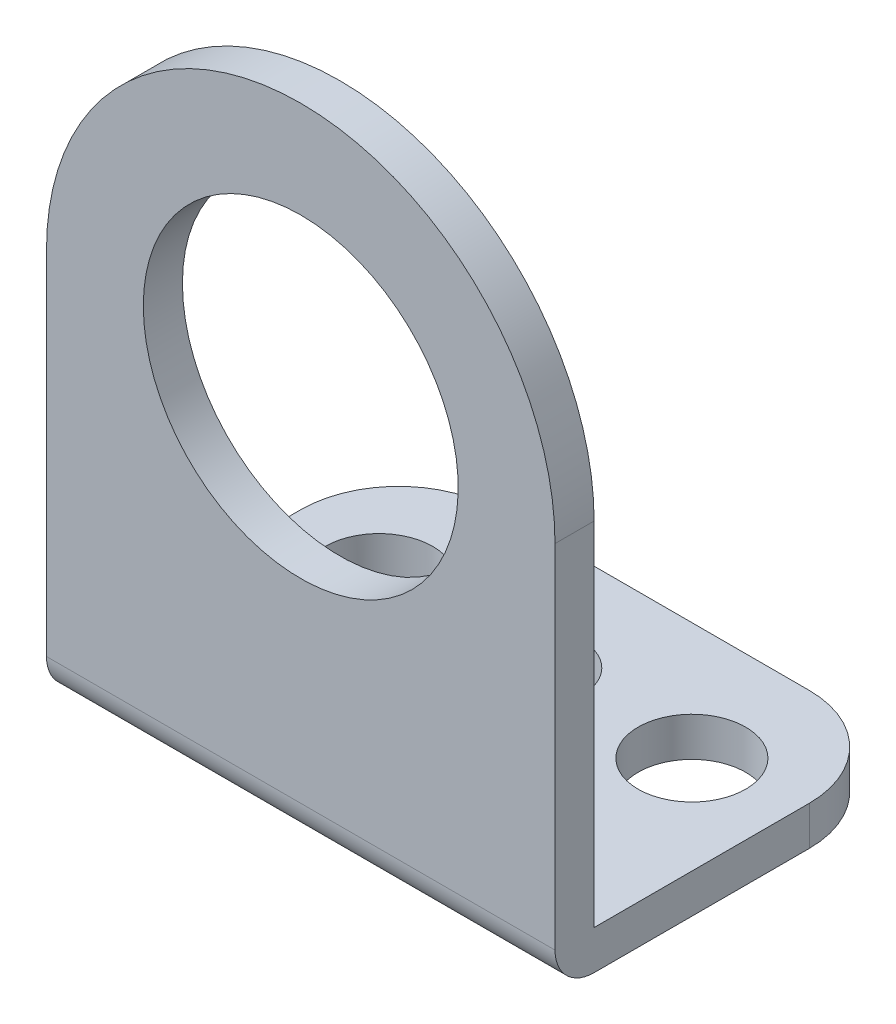
SolidWorks part; units mm, degrees
material "Al 6201"
ref_plane "Front Plane" through (0, 0, 0) normal (0, 0, 1) x (1, 0, 0)
ref_plane "Top Plane" through (0, 0, 0) normal (0, 1, 0) x (1, 0, 0)
ref_plane "Right Plane" through (0, 0, 0) normal (1, 0, 0) x (0, 0, -1)
sketch "Sketch1" plane through (0, 0, 0) normal (1, 0, 0) x (0, 0, -1)
  line L1 (0, 7.5) -> (2, 7.5)
  line L2 (0, 7.5) -> (0, 0)
  line L4 (2, 7.5) -> (2, 2)
  line L5 (2, 2) -> (18, 2)
  line L7 (0, 0) -> (18, 0)
  line L8 (18, 2) -> (18, 0)
  dimension "D1" = 7.5
  dimension "D2" = 18
  dimension "D3" = 2
extrude "Boss-Extrude1" add sketch "Sketch1" along normal mid plane 26
sketch "Sketch12" plane through (0, 0, -2) normal (0, 0, -1) x (-1, 0, 0)
  line L1 (0, 0) -> (0, 50000) construction
  line L3 (-13, 7.5) -> (13, 7.5) construction
  line L4 (-13, 0) -> (13, 0) construction
  line L6 (0, 20) -> (14.6033, 20) construction
  line L7 (0, 20) -> (-14.6033, 20) construction
  line L8 (13, 20) -> (13, 7.5)
  line L9 (13, 7.5) -> (-13, 7.5)
  line L10 (-13, 7.5) -> (-13, 20)
  circle A1 centre (0, 20) radius 8.05
  arc A2 (-13, 20) -> (13, 20) centre (0, 20) cw
  point P15 (0, 7.5)
  dimension "D3" = 16.1
  dimension "D1" = 20
extrude "Boss-Extrude2" add sketch "Sketch12" against normal up to surface (2 mm away) up to face at (0, 3.75, 0)
fillet "Fillet3" radius 2 1 edges at (0, 0, 0)
sketch "Sketch4" plane through (0, 0, -2) normal (0, 0, -1) x (-1, 0, 0)
  line L2 (0, 0) -> (0, 50000) construction
ref_plane "Plane1" through (0, 0, 0) normal (0, 0.7071, 0.7071) x (-1, 0, 0)
sketch "Sketch14" plane through (0, 0, 0) normal (0, 0.7071, 0.7071) x (-1, 0, 0)
  line L0 (0, 0) -> (0, 50000) construction
  line L1 (8.5, -2.8284) -> (11, -7.1586)
  line L2 (11, -7.1586) -> (13.5, -2.8284)
  line L3 (-13, -2.8284) -> (13, -2.8284) construction
  line L4 (8.5, -2.8284) -> (13.5, -2.8284)
  line L5 (11, -7.1586) -> (11, -10.5643) construction
  line L6 (-8.5, -2.8284) -> (-11, -7.1586)
  line L7 (-8.5, -2.8284) -> (-13.5, -2.8284)
  line L8 (-11, -7.1586) -> (-13.5, -2.8284)
  dimension "D1" = 22
  dimension "D2" = 5
  dimension "D3" = 60
sketch "Sketch15" plane through (0, 2, 0) normal (0, 1, 0) x (1, 0, 0)
  line L0 (0, 18) -> (0, 12) construction
  line L1 (13, 18) -> (-13, 18) construction
  line L2 (0, 12) -> (8, 12) construction
  circle A0 centre (0, 12) radius 2.4
  circle A1 centre (8, 12) radius 2.75
  circle A2 centre (-8, 12) radius 2.75
extrude "Cut-Extrude1" cut sketch "Sketch15" against normal up to surface (2 mm away) up to face at (0, 0, -10)
fillet "Fillet4" radius 5 2 edges at (13, 1, -18) (-13, 1, -18)
sketch "Sketch16" plane through (0, 2, 0) normal (0, 1, 0) x (1, 0, 0)
  line L0 (0, 12) -> (8, 12) construction
  line L1 (8, 12) -> (4, 12) construction
  line L2 (4, 12) -> (4, 2) construction
  line L3 (13, 2) -> (-13, 2) construction
  line L4 (0, 12) -> (0, 9.6) construction
  line L5 (-4, 12) -> (-4, 2) construction
  circle A0 centre (0, 12) radius 2.4 construction
ref_plane "Plane2" through (4, 0, 0) normal (1, 0, 0) x (0, 0, -1)
sketch "Sketch17" plane through (4, 0, 0) normal (1, 0, 0) x (0, 0, -1)
  line L0 (2, 2) -> (7, 2) construction
  line L1 (2, 2) -> (2, 7) construction
  line L2 (2, -200000) -> (2, 250000) construction
  line L3 (2, 7) -> (7, 2)
rib "Rib1" sketch "Sketch17" sketch "Sketch17" thickness 2 extrusion direction parallel to sketch draft on yes draft angle 30 parameters "D1"=2, "D3"=30
ref_plane "Plane3" through (-4, 0, 0) normal (1, 0, 0) x (0, 0, -1)
sketch "Sketch18" plane through (-4, 0, 0) normal (1, 0, 0) x (0, 0, -1)
  line L0 (2, 7) -> (7, 2) construction
  line L1 (2, 7) -> (7, 2)
rib "Rib2" sketch "Sketch18" sketch "Sketch18" thickness 2 extrusion direction parallel to sketch draft on yes draft angle 30 parameters "D1"=2, "D3"=30
